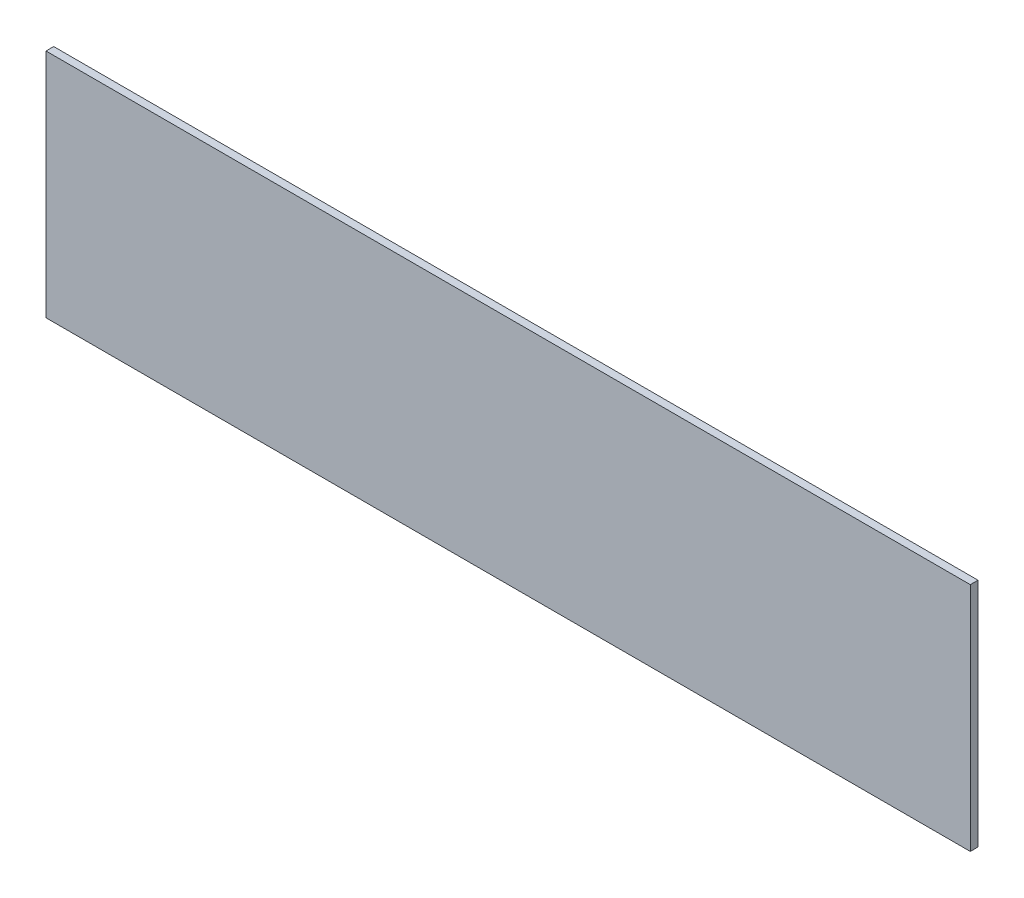
SolidWorks part; units mm, degrees
ref_plane "Front Plane" through (0, 0, 0) normal (0, 0, 1) x (1, 0, 0)
ref_plane "Top Plane" through (0, 0, 0) normal (0, 1, 0) x (1, 0, 0)
ref_plane "Right Plane" through (0, 0, 0) normal (1, 0, 0) x (0, 0, -1)
sketch "Sketch1" plane through (0, 0, 0) normal (0, 0, 1) x (1, 0, 0)
  line L1 (-152.4, 38.1) -> (152.4, 38.1)
  line L2 (-152.4, 38.1) -> (-152.4, -38.1)
  line L3 (-152.4, -38.1) -> (152.4, -38.1)
  line L4 (152.4, 38.1) -> (152.4, -38.1)
  line L5 (-152.4, 38.1) -> (152.4, -38.1) construction
  line L6 (-152.4, -38.1) -> (152.4, 38.1) construction
  point P0 (0, 0)
  dimension "D1" = 304.8
  dimension "D2" = 76.2
extrude "Boss-Extrude1" add sketch "Sketch1" along normal blind 2.54
